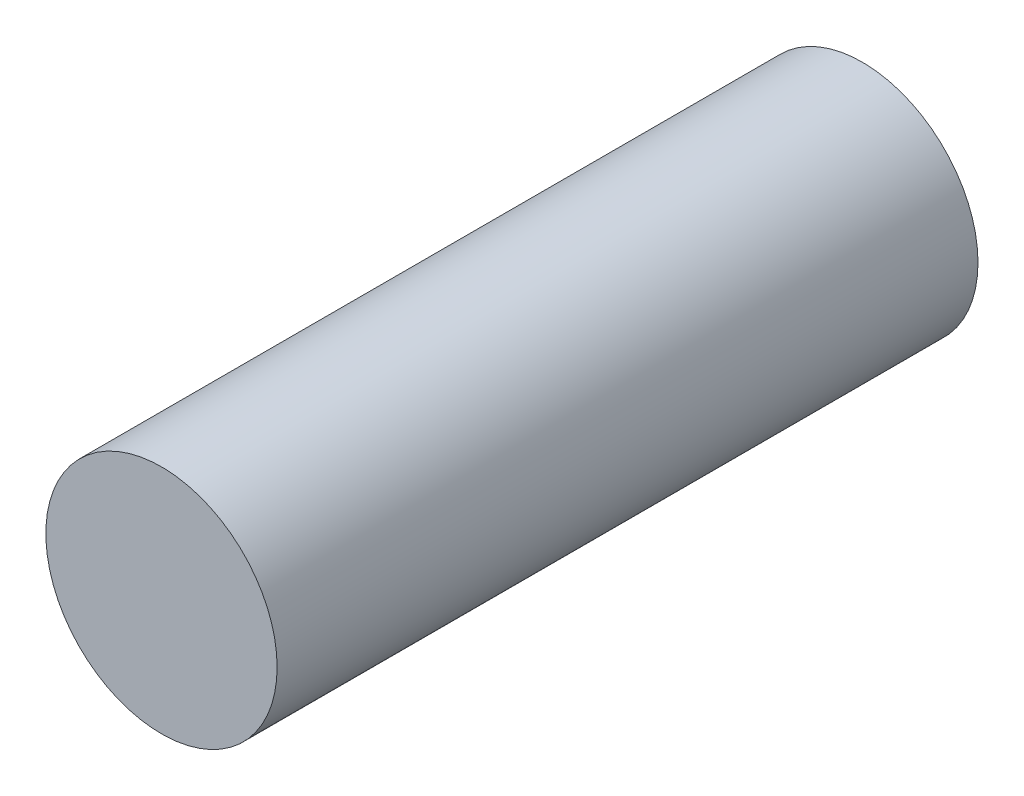
SolidWorks part; units mm, degrees
ref_plane "Přední rovina" through (0, 0, 0) normal (0, 0, 1) x (1, 0, 0)
ref_plane "Horní rovina" through (0, 0, 0) normal (0, 1, 0) x (1, 0, 0)
ref_plane "Pravá rovina" through (0, 0, 0) normal (1, 0, 0) x (0, 0, -1)
sketch "Skica1" plane through (0, 0, 0) normal (0, 0, 1) x (1, 0, 0)
  circle A0 centre (0, 0) radius 1.65
  dimension "D1" = 3.3
extrude "Přidat vysunutím1" add sketch "Skica1" along normal blind 10
